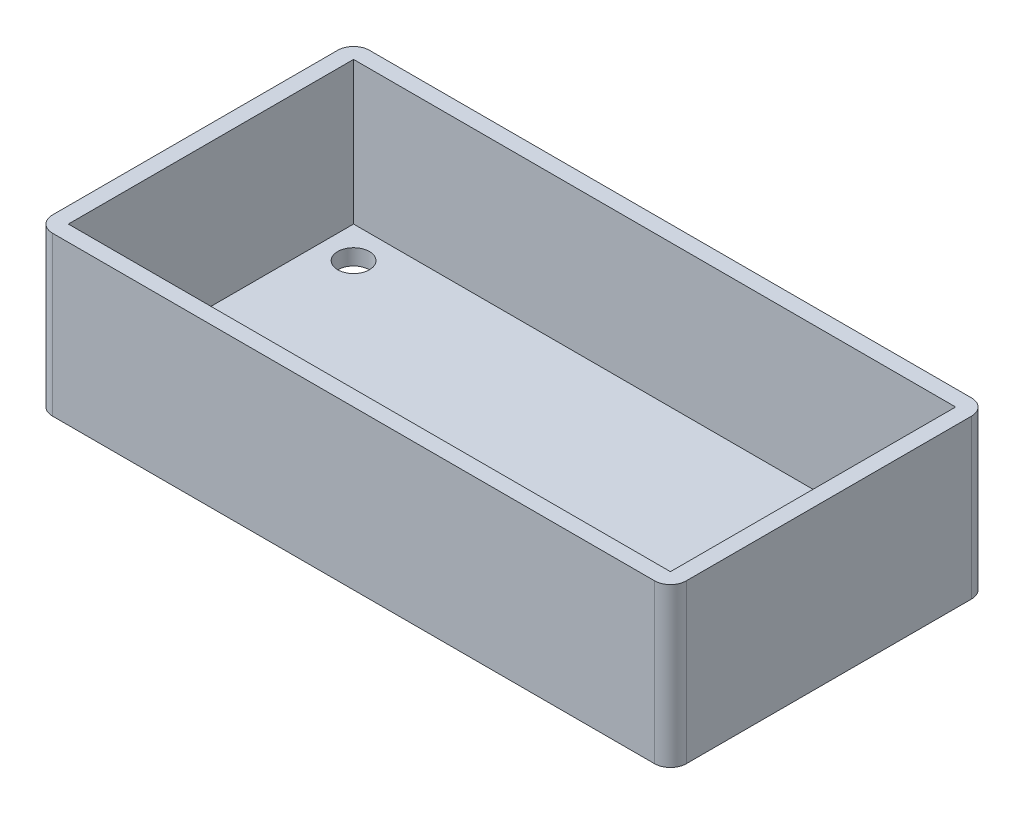
SolidWorks part; units mm, degrees
ref_plane "Front Plane" through (0, 0, 0) normal (0, 0, 1) x (1, 0, 0)
ref_plane "Top Plane" through (0, 0, 0) normal (0, 1, 0) x (1, 0, 0)
ref_plane "Right Plane" through (0, 0, 0) normal (1, 0, 0) x (0, 0, -1)
sketch "Sketch1" plane through (0, 0, 0) normal (0, 1, 0) x (1, 0, 0)
  line L1 (100, -50) -> (-100, -50)
  line L2 (100, -50) -> (100, 50)
  line L3 (100, 50) -> (-100, 50)
  line L4 (-100, -50) -> (-100, 50)
  line L5 (100, -50) -> (-100, 50) construction
  line L6 (100, 50) -> (-100, -50) construction
  point P0 (0, 0)
  dimension "base_l" = 200
  dimension "D1" = 100
extrude "Boss-Extrude1" add sketch "Sketch1" along normal blind 50
shell "Shell1" thickness 5
fillet "Fillet1" radius 5 4 edges at (100, 25, -50) (100, 25, 50) (-100, 25, 50) (-100, 25, -50)
sketch "Sketch5" plane through (0, 5, 0) normal (0, 1, 0) x (1, 0, 0)
  line L0 (-95, 45) -> (-95, -45) construction
  line L1 (95, 45) -> (-95, 45) construction
  line L2 (-95, -45) -> (95, -45) construction
  line L4 (95, -45) -> (95, 45) construction
  circle A0 centre (-85, 35) radius 5
  circle A1 centre (85, 35) radius 5
  circle A2 centre (85, -35) radius 5
  circle A3 centre (-85, -35) radius 5
  point P8 (0, 0)
  point P13 (0, 0)
  point P14 (0, 0)
  point P15 (0, 0)
  point P16 (0, 0)
  point P17 (53.1105, 35)
  point P18 (0, 0)
  point P19 (0, 0)
  point P22 (0, 0)
  dimension "D1" = 10
  dimension "D2" = 10
  dimension "D3" = 10
  dimension "D4" = 10
  dimension "D5" = 10
extrude "Cut-Extrude1" cut sketch "Sketch5" against normal through all
equation "\"D1@Sketch1\"=\"base_l\"/2"
equation "\"D1@Boss-Extrude1\"=\"base_l\"/4"
equation "\"D1@Shell1\"=\"base_l\"/40"
equation "\"D2@Sketch5\"=\"base_l\"/20"
equation "\"D3@Sketch5\"=\"base_l\"/20"
equation "\"D4@Sketch5\"=\"base_l\"/20"
equation "\"D5@Sketch5\"=\"base_l\"/20"
